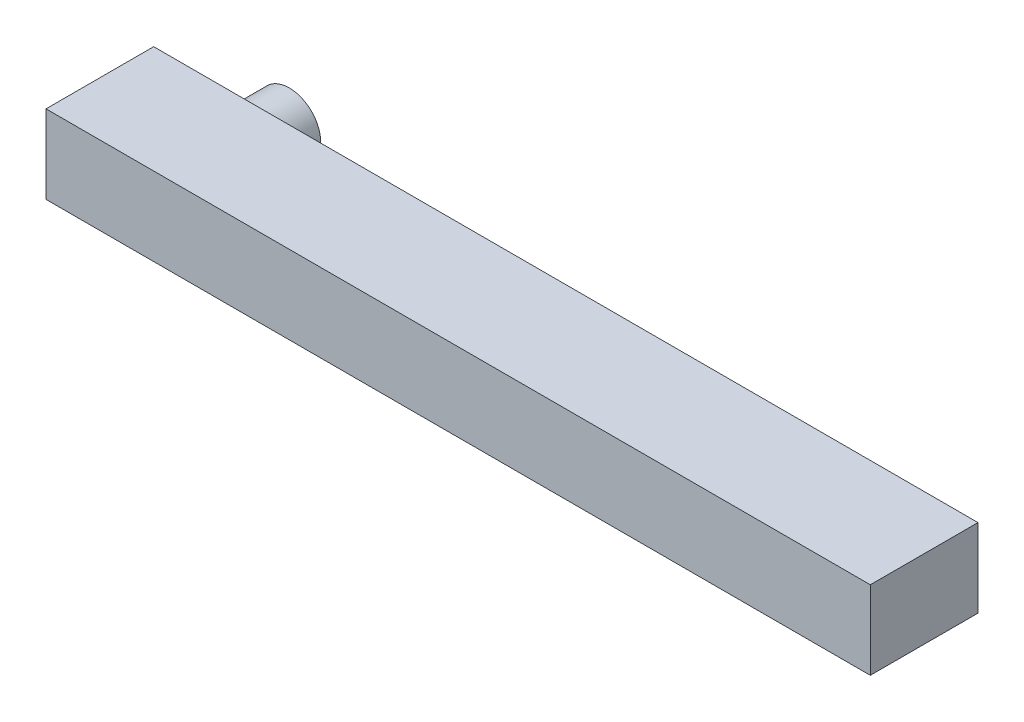
SolidWorks part; units mm, degrees
ref_plane "Front Plane" through (0, 0, 0) normal (0, 0, 1) x (1, 0, 0)
ref_plane "Top Plane" through (0, 0, 0) normal (0, 1, 0) x (1, 0, 0)
ref_plane "Right Plane" through (0, 0, 0) normal (1, 0, 0) x (0, 0, -1)
sketch "Sketch1" plane through (0, 0, 0) normal (0, 0, 1) x (1, 0, 0)
  line L0 (-31, 0) -> (31, 0)
  line L1 (31, 0) -> (31, 5.9)
  line L2 (31, 5.9) -> (-31, 5.9)
  line L3 (-31, 5.9) -> (-31, 0)
  point P4 (0, 0)
  dimension "D1" = 62
  dimension "D2" = 5.9
extrude "Boss-Extrude1" add sketch "Sketch1" against normal blind 8.1
sketch "Sketch4" plane through (0, 0, -8.1) normal (0, 0, -1) x (-1, 0, 0)
  line L0 (31, 2.95) -> (23.8, 2.95) construction
  line L1 (31, 5.9) -> (31, 0) construction
  circle A0 centre (23.8, 2.95) radius 2.365
  dimension "D2" = 4.73
  dimension "D1" = 7.2
extrude "Boss-Extrude2" add sketch "Sketch4" along normal blind 3
